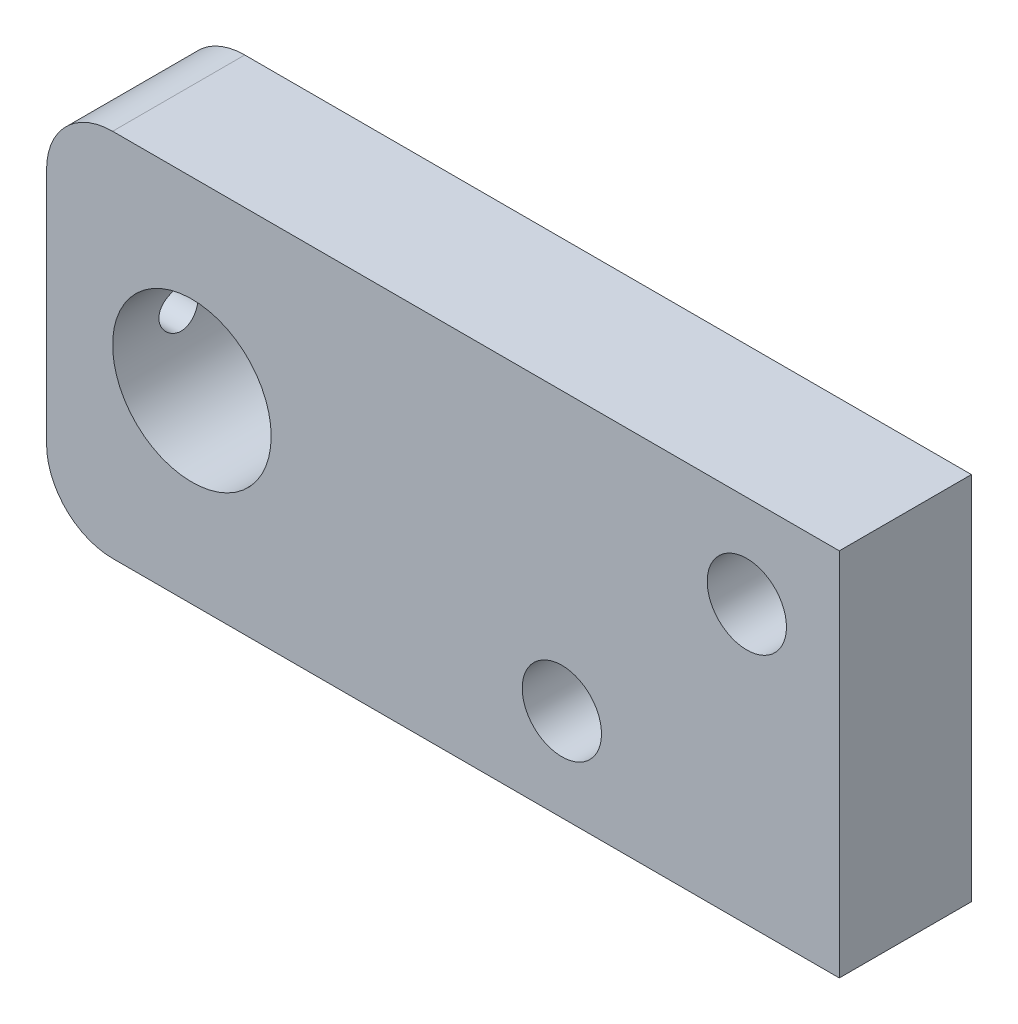
SolidWorks part; units mm, degrees
ref_plane "Ön Düzlem" through (0, 0, 0) normal (0, 0, 1) x (1, 0, 0)
ref_plane "Üst Düzlem" through (0, 0, 0) normal (0, 1, 0) x (1, 0, 0)
ref_plane "Sağ Düzlem" through (0, 0, 0) normal (1, 0, 0) x (0, 0, -1)
sketch "Çizim1" plane through (0, 0, 0) normal (0, 0, 1) x (1, 0, 0)
  line L1 (30, -14) -> (-25, -14)
  line L2 (30, -14) -> (30, 14)
  line L3 (30, 14) -> (-25, 14)
  line L4 (-30, -9) -> (-30, 9)
  line L5 (30, -14) -> (-30, 14) construction
  line L6 (30, 14) -> (-30, -14) construction
  line L7 (9, -7) -> (23, -7) construction
  line L8 (9, -7) -> (9, 7) construction
  line L9 (9, 7) -> (23, 7) construction
  line L10 (23, -7) -> (23, 7) construction
  line L11 (9, -7) -> (23, 7) construction
  line L12 (9, 7) -> (23, -7) construction
  arc A0 (-25, -14) -> (-30, -9) centre (-25, -9) cw
  arc A1 (-25, 14) -> (-30, 9) centre (-25, 9) ccw
  circle A2 centre (23, 7) radius 3
  circle A4 centre (-19, 0) radius 6
  circle A6 centre (9, -7) radius 3
  point P0 (0, 0)
  point P14 (0, 0)
  point P15 (16, 0)
  point P19 (-72.4281, 14)
  point P22 (30, 0)
  dimension "D2" = 5
  dimension "D4" = 14
  dimension "D5" = 6
  dimension "D6" = 14
  dimension "D8" = 12
  dimension "D1" = 60
  dimension "D3" = 28
  dimension "D7" = 35
extrude "Yükseklik-Ekstrüzyon1" add sketch "Çizim1" along normal blind 10
sketch "Çizim2" plane through (-30, 0, 0) normal (-1, 0, 0) x (0, 0, 1)
  line L0 (0, 9) -> (10, 9) construction
  circle A0 centre (5, 0) radius 1.5
  point P7 (5, 9)
  dimension "D1" = 3
extrude "Kes-Ekstrüzyon1" cut sketch "Çizim2" against normal up to next
